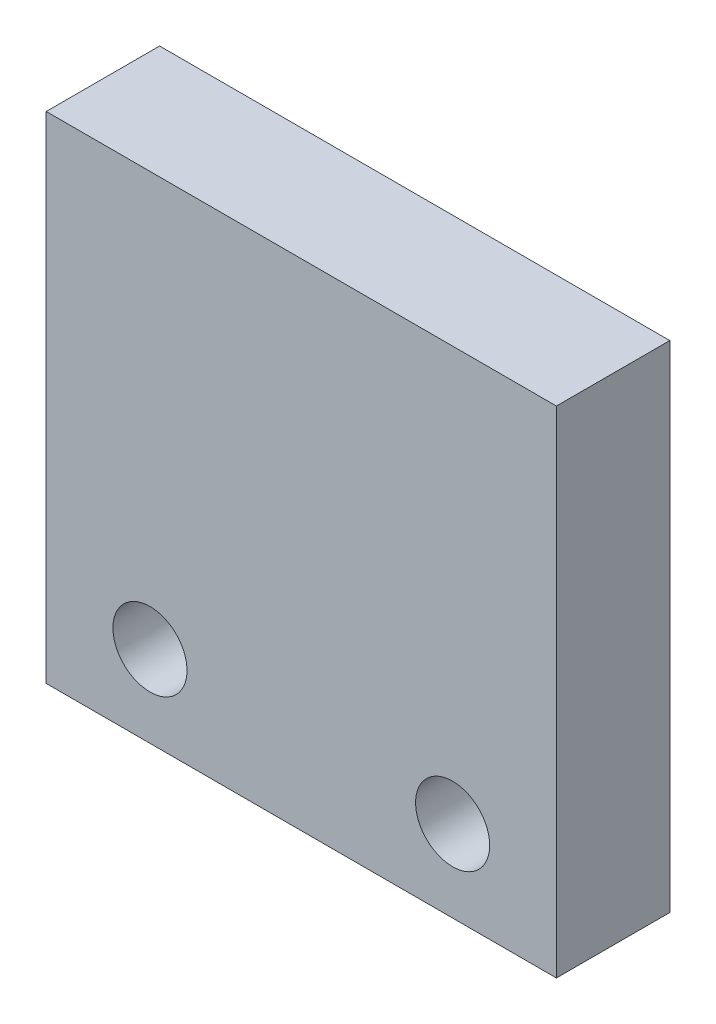
SolidWorks part; units mm, degrees
ref_plane "Front Plane" through (0, 0, 0) normal (0, 0, 1) x (1, 0, 0)
ref_plane "Top Plane" through (0, 0, 0) normal (0, 1, 0) x (1, 0, 0)
ref_plane "Right Plane" through (0, 0, 0) normal (1, 0, 0) x (0, 0, -1)
sketch "Sketch1" plane through (0, 0, 0) normal (0, 0, 1) x (1, 0, 0)
  line L1 (-17.21, 16.71) -> (17.21, 16.71)
  line L3 (-17.21, -16.71) -> (17.21, -16.71)
  line L4 (17.21, 16.71) -> (17.21, -16.71)
  line L5 (0, -16.71) -> (0, 16.71) construction
  line L9 (-17.21, 16.71) -> (-17.21, -16.71)
  circle A0 centre (10.21, -11.21) radius 2.5
  circle A1 centre (-10.21, -11.21) radius 2.5
  point P0 (-17.21, -16.71)
  point P6 (0, 0)
  dimension "D8" = 5
  dimension "D1" = 34.42
  dimension "D2" = 33.42
  dimension "D6" = 5.5
  dimension "D7" = 7
extrude "Boss-Extrude1" add sketch "Sketch1" along normal blind 7.65
